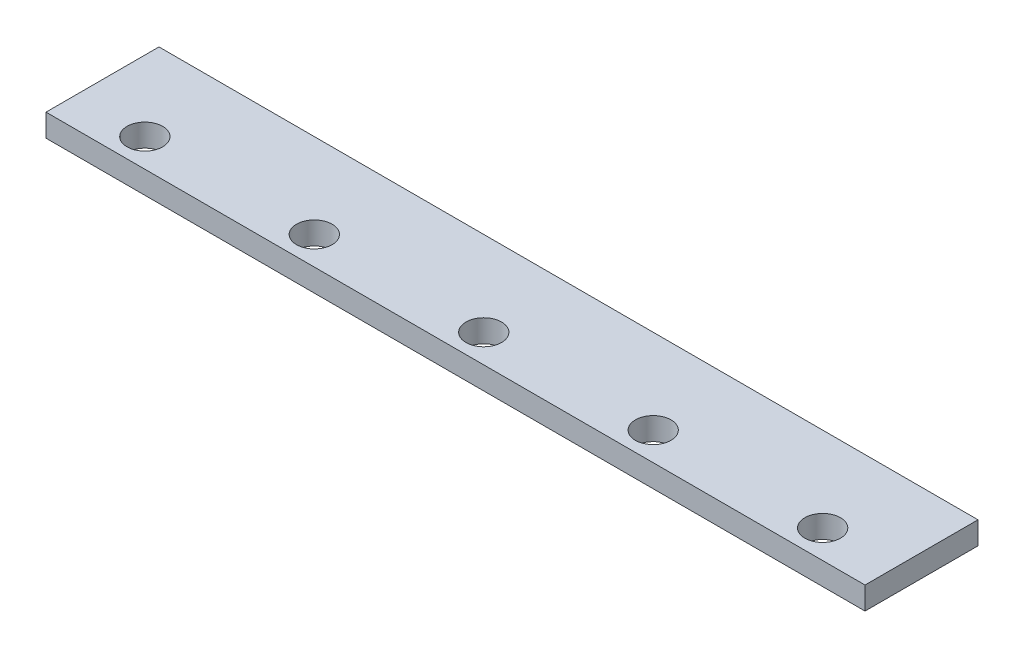
SolidWorks part; units mm, degrees
ref_plane "Front Plane" through (0, 0, 0) normal (0, 0, 1) x (1, 0, 0)
ref_plane "Top Plane" through (0, 0, 0) normal (0, 1, 0) x (1, 0, 0)
ref_plane "Right Plane" through (0, 0, 0) normal (1, 0, 0) x (0, 0, -1)
sketch "Sketch1" plane through (0, 0, 0) normal (0, 1, 0) x (1, 0, 0)
  line L1 (-290, 40) -> (290, 40)
  line L2 (-290, 40) -> (-290, -40)
  line L3 (-290, -40) -> (290, -40)
  line L4 (290, 40) -> (290, -40)
  line L5 (-290, 40) -> (290, -40) construction
  line L6 (-290, -40) -> (290, 40) construction
  point P0 (0, 0)
  dimension "D1" = 80
  dimension "D2" = 580
extrude "Boss-Extrude1" add sketch "Sketch1" along normal blind 16
sketch "Sketch2" plane through (0, 16, 0) normal (0, 1, 0) x (1, 0, 0)
  line L0 (-290, 40) -> (-290, -40) construction
  line L2 (-290, -40) -> (290, -40) construction
  circle A0 centre (-240, -20) radius 12.6
  point P6 (-245.5446, 62.7958)
  dimension "D1" = 12.6
  dimension "D2" = 50
  dimension "D3" = 20
extrude "Cut-Extrude1" cut sketch "Sketch2" against normal blind 16
pattern_linear "LPattern2" count 5 spacing 120 along (1, 0, 0) of "Cut-Extrude1"
